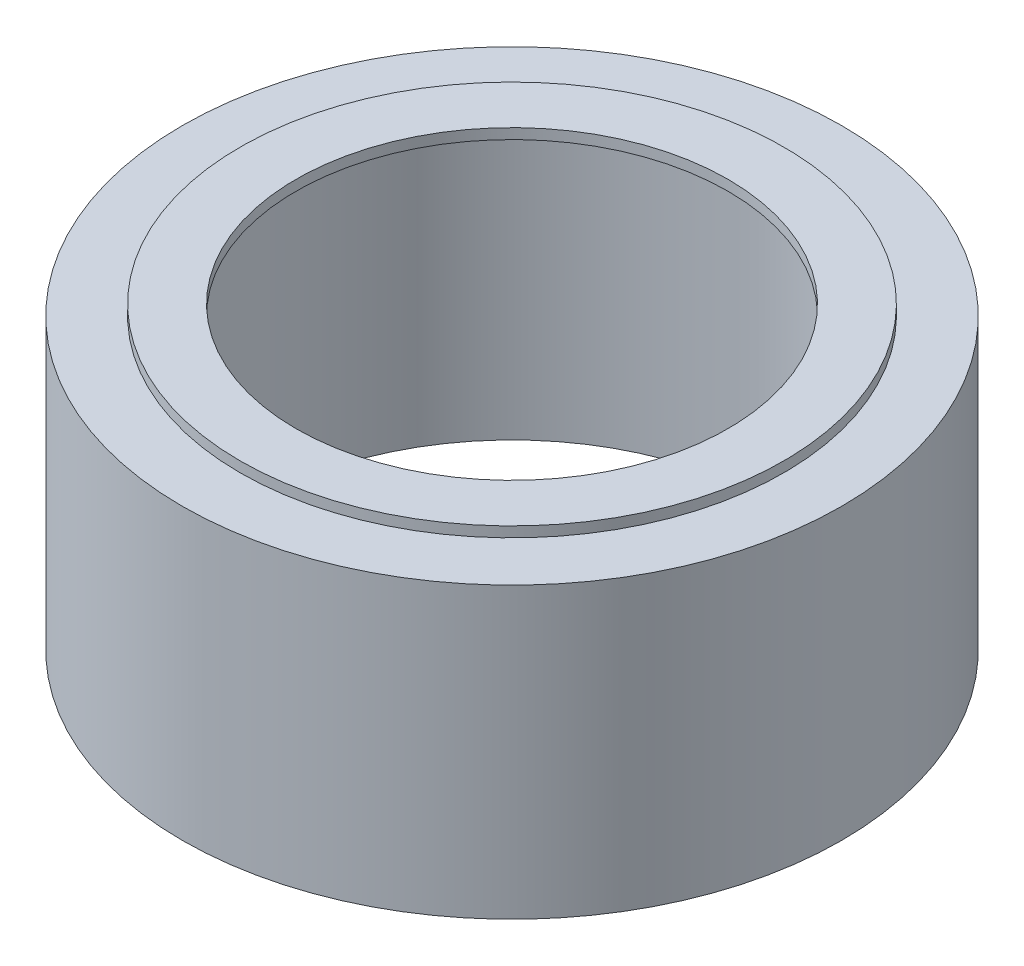
SolidWorks part; units mm, degrees
ref_plane "Front Plane" through (0, 0, 0) normal (0, 0, 1) x (1, 0, 0)
ref_plane "Top Plane" through (0, 0, 0) normal (0, 1, 0) x (1, 0, 0)
ref_plane "Right Plane" through (0, 0, 0) normal (1, 0, 0) x (0, 0, -1)
sketch "Sketch2" plane through (0, 0, 0) normal (0, 1, 0) x (1, 0, 0)
  circle A0 centre (0, 0) radius 10.355 construction
  circle A1 centre (0, 0) radius 15.95
  circle A2 centre (0, 0) radius 12.45
  dimension "D1" = 20.71
  dimension "D2" = 31.9
  dimension "D3" = 3.5
extrude "Boss-Extrude1" add sketch "Sketch2" along normal blind 14
sketch "Sketch3" plane through (0, 14, 0) normal (0, 1, 0) x (1, 0, 0)
  circle A0 centre (0, 0) radius 13.15
  circle A1 centre (0, 0) radius 12.45
  circle A2 centre (0, 0) radius 10.45
  circle A3 centre (0, 0) radius 12.45 construction
  circle M5 centre (0, 0) radius 12.45
  dimension "D1" = 2
  dimension "D2" = 0.7
extrude "Boss-Extrude2" add sketch "Sketch3" along normal blind 0.5 separate body contours A2 M5 | A0 M5
